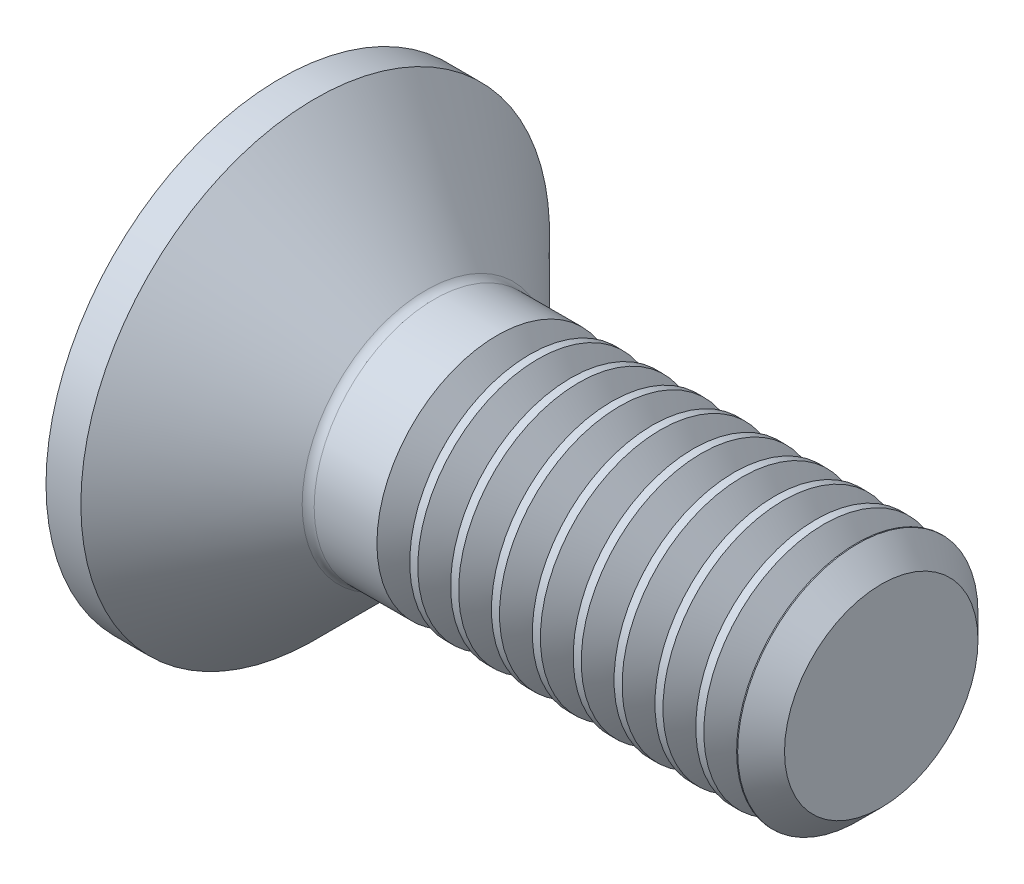
SolidWorks part; units mm, degrees
ref_plane "Plane1" through (0, 0, 0) normal (0, 0, 1) x (1, 0, 0)
ref_plane "Plane2" through (0, 0, 0) normal (0, 1, 0) x (1, 0, 0)
ref_plane "Plane3" through (0, 0, 0) normal (1, 0, 0) x (0, 0, -1)
sketch "BodySke" plane through (0, 0, 0) normal (0, 0, 1) x (1, 0, 0)
  line L0 (0, 0) -> (0, 3.9)
  line L1 (0.58, 3.9) -> (2.48, 2)
  line L2 (0, 3.9) -> (0.58, 3.9)
  line L3 (2.48, 2) -> (9.61, 2)
  line L4 (10, 1.61) -> (10, 0)
  line L5 (10, 0) -> (0, 0)
  line L6 (0, 0) -> (127, 0) construction
  line L7 (0.58, -3.9) -> (2.48, -2) construction
  line L8 (10, 1.61) -> (9.61, 2)
  line L9 (0, -3.9) -> (0.58, -3.9) construction
  line L10 (10, -1.61) -> (9.61, -2) construction
  line L11 (3.18, 8.35) -> (3.18, -13.875) construction
  line L12 (0, 19.05) -> (0, -3.175) construction
  dimension "D1" = 0.58
  dimension "Diameter" = 4
  dimension "Head_ht" = 2.48
  dimension "Length" = 10
  dimension "Body_ch_ang" = 45
  dimension "Head_dia" = 7.8
  dimension "Minor_dia" = 3.22
  dimension "Head_ang" = 90
  dimension "Advance" = 0.7
  dimension "Thread_nom" = 10
revolve "BaseBody" add sketch "BodySke" angle 360 about L6
cosmetic thread "ThreadCosmetic" [suppressed] parameters "Thread_length"=6.12, "Thread_minor"=3.22
fillet "Fillet1" radius 0.2 1 edges at (2.48, 0, 2)
sketch "Sketch2" plane through (0, 0, 0) normal (0, 0, 1) x (1, 0, 0)
  line L0 (0, 1.25) -> (1.5, 1.25)
  line L1 (1.5, 1.25) -> (2.2217, 0)
  line L2 (0, 0) -> (127, 0) construction
  line L3 (2.2217, 0) -> (0, 0)
  line L4 (0, 0) -> (0, 1.25)
  line L5 (0, -1.25) -> (1.5, -1.25) construction
  line L6 (0, 0) -> (47.625, 0) construction
  line L8 (0, 3.9) -> (0, -3.9) construction
  dimension "D2" = 60
  dimension "PreBroach_depth" = 1.5
  dimension "PreBroach_dia" = 2.5
revolve "PreBroach" cut sketch "Sketch2" angle 360 about L6
sketch "Sketch3" plane through (0, 0, 0) normal (-1, 0, 0) x (0, 0, 1)
  line L0 (-1.25, -0.7217) -> (-1.25, 0.7217)
  line L1 (-1.25, 0.7217) -> (0, 1.4434)
  line L2 (0, 1.4434) -> (1.25, 0.7217)
  line L3 (1.25, 0.7217) -> (1.25, -0.7217)
  line L4 (1.25, -0.7217) -> (0, -1.4434)
  line L5 (0, -1.4434) -> (-1.25, -0.7217)
  dimension "D1" = 1.25
  dimension "D2" = 1.25
  dimension "D3" = 2.5
  dimension "Hex_size" = 2.5
extrude "Hex" cut sketch "Sketch3" against normal blind 1.5
sketch "ThdSchSke" plane through (0, 0, 0) normal (0, 0, 1) x (1, 0, 0)
  line L0 (3.88, -1.61) -> (3.6069, -2)
  line L1 (3.88, -1.61) -> (4.1531, -2)
  line L2 (4.1531, -2) -> (4.1531, -2.5)
  line L3 (-3.175, 0) -> (5.1513, 0) construction
  line L4 (0, 3.9) -> (0, -3.9) construction
  line L5 (4.1531, -2.5) -> (3.6069, -2.5)
  line L6 (3.6069, -2.5) -> (3.6069, -2)
  dimension "Thread_minor" = 3.22
  dimension "Diameter" = 4
  dimension "Start" = 3.88
  dimension "SideAngle" = 55
  dimension "VeeAngle" = 70
  dimension "Overcut" = 5
revolve "ThreadSchematic" cut sketch "ThdSchSke" angle 360 about L3
pattern_linear "ThdSchPat" count 9 spacing 0.68 along (1, 0, 0) of "ThreadSchematic"
equation "\"Thread_minor@ThreadCosmetic\"  =  \"Minor_dia@BodySke\""
equation "\"D1@Sketch3\" = \"Hex_size@Sketch3\" / 2"
equation "\"D2@Sketch3\" = \"D1@Sketch3\""
equation "\"D3@Sketch3\" = \"Hex_size@Sketch3\""
equation "\"Thread_length@ThreadCosmetic\" = ((sgn( (\"Length@BodySke\" - \"Advance@BodySke\" * 2.0 - \"Head_ht@BodySke\" ) - \"Thread_nom@BodySke\" )-1)*( (\"Length@BodySke\" - \"Advance@BodySke\" * 2.0 - \"Head_ht@BodySke\" ) - \"Thread_nom@BodySke\" ))/-2+ \"Thread_nom@BodySke\""
equation "\"Thread_minor@ThdSchSke\" = \"Minor_dia@BodySke\""
equation "\"Diameter@ThdSchSke\" = \"Diameter@BodySke\""
equation "\"Overcut@ThdSchSke\" = \"Diameter@BodySke\" * 1.25"
equation "\"Start@ThdSchSke\" = 0.000001 + \"Length@BodySke\" - \"Thread_length@ThreadCosmetic\"  '---Countersunk---"
equation "\"Num_threads@ThdSchPat\" = int( \"Thread_length@ThreadCosmetic\" / \"Advance@BodySke\" + 0.999 )  + 1"
equation "\"Advance@ThdSchPat\" = \"Thread_length@ThreadCosmetic\" /  (\"Num_threads@ThdSchPat\" - 1) 'relax it"
equation "\"Num_threads@ThdSchPat\" = \"Num_threads@ThdSchPat\" - sgn( \"Num_threads@ThdSchPat\" - 1) '---chamfered tips only---"
